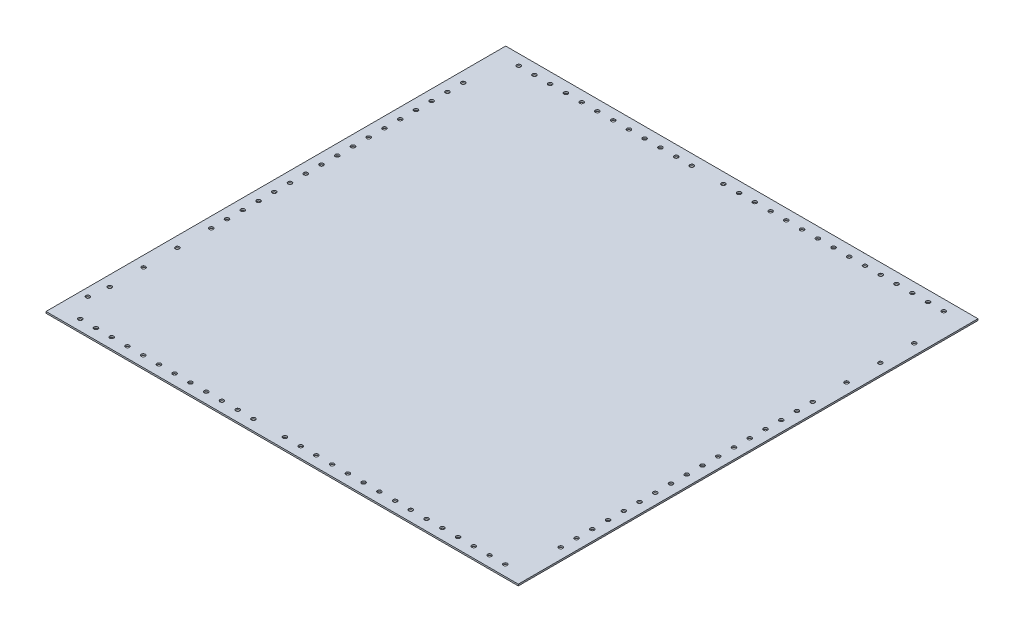
SolidWorks part; units mm, degrees
ref_plane "Front Plane" through (0, 0, 0) normal (0, 0, 1) x (1, 0, 0)
ref_plane "Top Plane" through (0, 0, 0) normal (0, 1, 0) x (1, 0, 0)
ref_plane "Right Plane" through (0, 0, 0) normal (1, 0, 0) x (0, 0, -1)
sketch "Sketch1" plane through (0, 0, 0) normal (0, 1, 0) x (1, 0, 0)
  line L1 (0, 0) -> (600, 0)
  line L2 (0, 0) -> (0, 584)
  line L3 (0, 584) -> (600, 584)
  line L4 (600, 0) -> (600, 584)
  dimension "D1" = 584
  dimension "D2" = 600
extrude "Boss-Extrude1" add sketch "Sketch1" along normal blind 2.032
hole_wizard "Ø5.0 (5) Diameter Hole2" positions "Sketch4" profile "Sketch2" hole size "Ø5.0" standard "ANSI Metric" end condition up to next
sketch "Sketch4" plane through (0, 2.032, 0) normal (0, 1, 0) x (1, 0, 0)
  point P0 (480.2665, -553.9619)
  point P1 (30, 13.4938)
  point P4 (50, 13.4938)
  point P7 (70, 13.4938)
  point P10 (90, 13.4938)
  point P13 (110, 13.4938)
  point P16 (130, 13.4938)
  point P19 (150, 13.4938)
  point P22 (170, 13.4938)
  point P25 (190, 13.4938)
  point P28 (210, 13.4938)
  point P31 (230, 13.4938)
  point P34 (250, 13.4938)
  point P37 (290, 13.4938)
  point P40 (310, 13.4938)
  point P43 (330, 13.4938)
  point P46 (350, 13.4938)
  point P49 (370, 13.4938)
  point P52 (390, 13.4938)
  point P55 (410, 13.4938)
  point P58 (430, 13.4938)
  point P61 (450, 13.4938)
  point P64 (470, 13.4938)
  point P67 (490, 13.4938)
  point P70 (510, 13.4938)
  point P73 (530, 13.4938)
  point P76 (550, 13.4938)
  point P79 (570, 13.4938)
  point P82 (586.5063, 67.5)
  point P85 (586.5063, 87.5)
  point P88 (586.5063, 107.5)
  point P91 (586.5063, 127.5)
  point P94 (586.5063, 147.5)
  point P97 (586.5063, 167.5)
  point P100 (586.5063, 187.5)
  point P103 (586.5063, 207.5)
  point P106 (586.5063, 227.5)
  point P109 (586.5063, 247.5)
  point P112 (586.5063, 267.5)
  point P115 (586.5063, 287.5)
  point P118 (586.5063, 307.5)
  point P121 (586.5063, 327.5)
  point P124 (586.5063, 347.5)
  point P127 (586.5063, 367.5)
  point P130 (586.5063, 387.5)
  point P133 (586.5063, 430.5)
  point P136 (586.5063, 473.5)
  point P139 (586.5063, 516.5)
  point P142 (570, 570.5062)
  point P145 (550, 570.5062)
  point P148 (530, 570.5062)
  point P151 (510, 570.5062)
  point P154 (490, 570.5062)
  point P157 (470, 570.5062)
  point P160 (450, 570.5062)
  point P163 (410, 570.5062)
  point P166 (430, 570.5062)
  point P169 (390, 570.5062)
  point P172 (370, 570.5062)
  point P175 (350, 570.5062)
  point P178 (330, 570.5062)
  point P181 (310, 570.5062)
  point P184 (290, 570.5062)
  point P187 (250, 570.5062)
  point P190 (210, 570.5062)
  point P193 (230, 570.5062)
  point P196 (190, 570.5062)
  point P199 (170, 570.5062)
  point P202 (150, 570.5062)
  point P205 (130, 570.5062)
  point P208 (110, 570.5062)
  point P211 (90, 570.5062)
  point P214 (70, 570.5062)
  point P217 (50, 570.5062)
  point P220 (30, 570.5062)
  point P223 (586.5063, 516.5)
sketch "Sketch2" plane through (480.2665, 2.032, 553.9619) normal (1, 0, 0) x (0, 0, 1)
  line L0 (0, 0) -> (0, 2.032)
  line L1 (0, 2.032) -> (2.5, 2.032)
  line L2 (2.5, 2.032) -> (2.5, 0.021)
  line L3 (2.5, 0.021) -> (2.525, 0)
  line L5 (2.525, 0) -> (0, 0)
  line L6 (-2.5, 0.021) -> (-2.525, 0) construction
  line L11 (0, -6.35) -> (0, 107.95) construction
  dimension "Thru Hole Dia." = 5
  dimension "Thru Hole Depth" = 2.032
  dimension "Near C'Sink Dia." = 5.05
  dimension "Near C'Sink Angle" = 100
hole_wizard "Ø5.0 (5) Diameter Hole3" positions "Sketch7" profile "Sketch6" hole size "Ø5.0" standard "ANSI Metric" end condition up to next
sketch "Sketch7" plane through (0, 2.032, 0) normal (0, 1, 0) x (1, 0, 0)
  point P0 (13.4938, 516.5)
  point P3 (13.4938, 496.5)
  point P6 (13.4938, 476.5)
  point P9 (13.4938, 456.5)
  point P12 (13.4938, 436.5)
  point P15 (13.4938, 416.5)
  point P18 (13.4938, 396.5)
  point P21 (13.4938, 376.5)
  point P24 (13.4938, 356.5)
  point P27 (13.4938, 336.5)
  point P30 (13.4938, 316.5)
  point P33 (13.4938, 296.5)
  point P36 (13.4938, 276.5)
  point P39 (13.4938, 256.5)
  point P42 (13.4938, 236.5)
  point P45 (13.4938, 216.5)
  point P48 (13.4937, 196.5)
  point P51 (13.4938, 153.5)
  point P54 (13.4937, 110.5)
  point P57 (13.4937, 67.5)
  point P60 (10.3759, 42.8625)
sketch "Sketch6" plane through (13.4938, 2.032, -516.5) normal (1, 0, 0) x (0, 0, 1)
  line L0 (0, 0) -> (0, 2.032)
  line L1 (0, 2.032) -> (2.5, 2.032)
  line L2 (2.5, 2.032) -> (2.5, 0.021)
  line L3 (2.5, 0.021) -> (2.525, 0)
  line L5 (2.525, 0) -> (0, 0)
  line L6 (-2.5, 0.021) -> (-2.525, 0) construction
  line L11 (0, -6.35) -> (0, 107.95) construction
  dimension "Thru Hole Dia." = 5
  dimension "Thru Hole Depth" = 2.032
  dimension "Near C'Sink Dia." = 5.05
  dimension "Near C'Sink Angle" = 100
